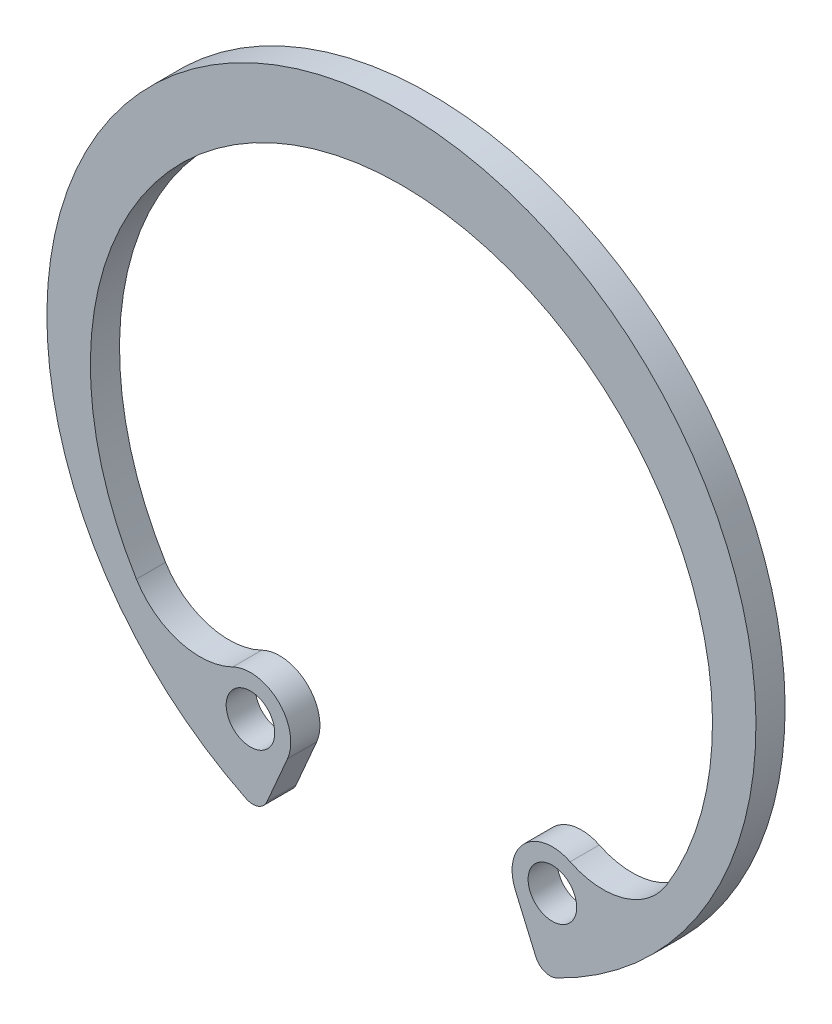
SolidWorks part; units mm, degrees
material "Stainless Steel (ferritic)"
ref_plane "Front Plane" through (0, 0, 0) normal (0, 0, 1) x (1, 0, 0)
ref_plane "Top Plane" through (0, 0, 0) normal (0, 1, 0) x (1, 0, 0)
ref_plane "Right Plane" through (0, 0, 0) normal (1, 0, 0) x (0, 0, -1)
sketch "Sketch1" plane through (0, 0, 0) normal (0, 0, 1) x (1, 0, 0)
  line L0 (0, 18.25) -> (0, 14.95) construction
  line L1 (-18.25, 0) -> (-16.6, 0) construction
  line L2 (0, 0) -> (0, -18.25) construction
  line L3 (-5.1, -11.7946) -> (-7.2432, -16.7511) construction
  line L4 (-5.1, -11.7946) -> (-7.6, -11.7946) construction
  circle A0 centre (0, 0) radius 17.85 construction
  circle A1 centre (0, 0) radius 18.25 construction
  circle A2 centre (0, 0) radius 17 construction
  dimension "Ring OD" = 36.5
  dimension "For ID" = 34
  dimension "Maximum Section" = 3.3
  dimension "Minimum Section" = 1.65
  dimension "Gap Width" = 10.2
  dimension "Lug Height" = 5.4
  dimension "Hole Diameter" = 2.5
sketch "Sketch2" plane through (0, 0, 0) normal (1, 0, 0) x (0, 0, -1)
  line L0 (-0.8, 18.25) -> (0.8, 18.25) construction
  line L1 (-0.75, -18.25) -> (0.75, -18.25) construction
  point P3 (0, 18.25)
  point P7 (0, -18.25)
  point P8 (-0.75, -18.25)
  point P10 (0.75, -18.25)
  point P11 (-0.8, 18.25)
  point P12 (0.8, 18.25)
  dimension "For Groove Width" = 1.6
  dimension "Ring Thickness" = 1.5
sketch "Sketch3" plane through (0, 0, 0) normal (0, 0, 1) x (1, 0, 0)
  line L0 (-7.2432, -16.7511) -> (-5.15, -11.9103) construction
  line L1 (-5.15, -11.9103) -> (-8.0805, -10.1232) construction
  line L2 (0, 0) -> (-6.6903, -10.971) construction
  line L3 (-13.6434, -9.4431) -> (0, 0) construction
  line L4 (0, 0) -> (0, -18.25) construction
  line L5 (-8.0805, -10.1232) -> (0, 0) construction
  line L6 (-6.6903, -10.971) -> (-7.7706, -12.7426) construction
  line L7 (-7.7706, -12.7426) -> (-8.8509, -14.5142) construction
  line L8 (0, 18.25) -> (0, 14.95) construction
  line L11 (-5.866, -13.5661) -> (-7.2432, -16.7511)
  line L12 (0, 0) -> (0, -18.25) construction
  line L13 (5.866, -13.5661) -> (7.2432, -16.7511)
  line L14 (-5.1, -11.7946) -> (-7.2432, -16.7511) construction
  line L15 (-6.6903, -10.971) -> (-9.5017, -15.5814) construction
  arc A0 (-7.2432, -16.7511) -> (7.2432, -16.7511) centre (0, 0) cw
  circle A1 centre (0, 0) radius 18.25 construction
  arc A2 (-13.6434, -9.4431) -> (13.6434, -9.4431) centre (0, -1.062) cw
  circle A4 centre (-7.7706, -12.7426) radius 1.25
  circle A5 centre (0, 0) radius 16.6 construction
  circle A7 centre (7.7706, -12.7426) radius 1.25
  circle A8 centre (0, 0) radius 17 construction
  arc A9 (-8.6843, -10.8796) -> (-5.866, -13.5661) centre (-7.7706, -12.7426) cw
  arc A10 (-13.6434, -9.4431) -> (-8.6843, -10.8796) centre (-10.374, -7.4347) ccw
  arc A11 (8.6843, -10.8796) -> (5.866, -13.5661) centre (7.7706, -12.7426) ccw
  arc A12 (13.6434, -9.4431) -> (8.6843, -10.8796) centre (10.374, -7.4347) cw
  point P3 (0, -18.25)
  dimension "D1" = 2.5
  dimension "D2" = 5.4
  dimension "D3" = 8.775
extrude "Boss-Extrude1" add sketch "Sketch3" against normal up to vertex (0.75 mm away) and the other way up to vertex (0.75 mm away) up to point (0, -18.25, -0.75) other way up to point (0, -18.25, 0.75)
fillet "Fillet1" radius 0.7937 2 edges at (7.2432, -16.7511, 0) (-7.2432, -16.7511, 0)
equation "\"D1@Sketch3\"=\"Hole Diameter@Sketch1\""
equation "\"Minimum Section@Sketch1\"=\"Maximum Section@Sketch1\"*.5"
equation "\"Gap Width@Sketch1\"=\"For ID@Sketch1\"*.3"
equation "\"D2@Sketch3\"=\"Lug Height@Sketch1\""
equation "\"D3@Sketch3\"=\"Lug Height@Sketch1\"*1.625"
